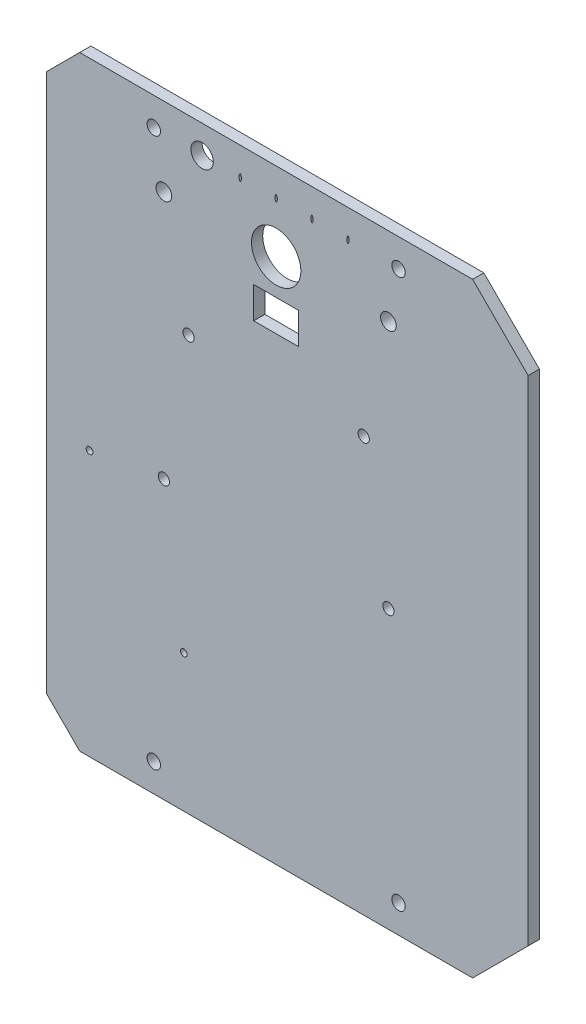
SolidWorks part; units mm, degrees
material "Alliage 1060"
ref_plane "Plan de dessus" through (0, 0, 0) normal (0, 0, 1) x (1, 0, 0)
ref_plane "Plan de droite" through (0, 0, 0) normal (0, 1, 0) x (1, 0, 0)
ref_plane "Plan de face" through (0, 0, 0) normal (1, 0, 0) x (0, 0, -1)
sketch "Esquisse1" plane through (0, 0, 0) normal (0, 0, 1) x (1, 0, 0)
  line L0 (0, 0) -> (-175, 0)
  line L1 (-175, 0) -> (-199.7487, 24.7487)
  line L2 (-199.7487, 24.7487) -> (-199.7487, 244.7487)
  line L3 (-199.7487, 244.7487) -> (-175, 269.4975)
  line L4 (-175, 269.4975) -> (0, 269.4975)
  line L5 (0, 269.4975) -> (24.7487, 244.7487)
  line L6 (24.7487, 244.7487) -> (24.7487, 24.7487)
  line L7 (24.7487, 24.7487) -> (0, 0)
  dimension "D1" = 220
  dimension "D2" = 35
  dimension "D3" = 135
  dimension "D4" = 175
extrude "Base" add sketch "Esquisse1" along normal blind 5
sketch "Esquisse2" plane through (0, 0, 5) normal (0, 0, 1) x (1, 0, 0)
  line L0 (-199.7487, 244.7487) -> (-199.7487, 24.7487) construction
  line L1 (-175, 0) -> (0, 0) construction
  line L2 (-199.7487, 134.7487) -> (24.7487, 134.7487) construction
  line L3 (24.7487, 24.7487) -> (24.7487, 244.7487) construction
  line L4 (-87.5, 269.4975) -> (-87.5, 0) construction
  line L5 (0, 269.4975) -> (-175, 269.4975) construction
  line L7 (-132.5, 179.7487) -> (-42.5, 179.7487) construction
  line L8 (-132.5, 179.7487) -> (-132.5, 89.7487) construction
  line L9 (-132.5, 89.7487) -> (-42.5, 89.7487) construction
  line L10 (-42.5, 179.7487) -> (-42.5, 89.7487) construction
  circle A0 centre (-141.9987, 12.5) radius 3
  circle A1 centre (-141.9987, 256.9975) radius 3
  circle A2 centre (-33.0013, 12.5) radius 3
  circle A3 centre (-33.0013, 256.9975) radius 3
  circle A4 centre (-137.5, 123.7487) radius 2.5
  circle A5 centre (-126.5, 184.7487) radius 2.5
  circle A6 centre (-37.5, 123.7487) radius 2.5
  circle A7 centre (-48.5, 184.7487) radius 2.5
  point P25 (-87.5, 179.7487)
  point P26 (-132.5, 134.7487)
  dimension "D1" = 6
  dimension "D6" = 5
  dimension "D8" = 5
  dimension "D2" = 57.75
  dimension "D3" = 12.5
  dimension "D4" = 90
  dimension "D5" = 34
  dimension "D7" = 5
  dimension "D9" = 5
  dimension "D10" = 6
  dimension "D11" = 90
sketch "Esquisse4" plane through (0, 0, 5) normal (0, 0, 1) x (1, 0, 0)
  line L0 (-87.5, 269.4975) -> (-87.5, 0) construction
  line L1 (0, 269.4975) -> (-175, 269.4975) construction
  line L2 (-132.5, 179.7487) -> (-42.5, 179.7487) construction
  line L3 (-97.5, 218.7487) -> (-77.5, 218.7487)
  line L4 (-97.5, 218.7487) -> (-97.5, 204.7487)
  line L5 (-97.5, 204.7487) -> (-77.5, 204.7487)
  line L6 (-77.5, 218.7487) -> (-77.5, 204.7487)
  line L7 (-87.5, 234.4975) -> (-37.5, 234.4975) construction
  line L8 (-87.5, 234.4975) -> (-137.5, 234.4975) construction
  line L9 (24.7487, 24.7487) -> (24.7487, 244.7487) construction
  circle A0 centre (-87.5, 234.4975) radius 11
  circle A1 centre (-137.5, 234.4975) radius 3.5
  circle A2 centre (-37.5, 234.4975) radius 3.5
  ellipse E0 centre (-103.5, 256.9975) end of major axis (-103.5, 255.4975) minor radius 0.5
  ellipse E5 centre (-87.5, 256.9975) end of major axis (-87.5, 255.4975) minor radius 0.5
  ellipse E6 centre (-71.5, 256.9975) end of major axis (-71.5, 255.4975) minor radius 0.5
  ellipse E7 centre (-55.5, 256.9975) end of major axis (-55.5, 255.4975) minor radius 0.5
  point P28 (-87.5, 218.7487)
  dimension "D4" = 22
  dimension "D7" = 7
  dimension "D1" = 3
  dimension "D2" = 1
  dimension "D3" = 16
  dimension "D5" = 35
  dimension "D8" = 35
  dimension "D10" = 25
  dimension "D11" = 14
  dimension "D12" = 20
  dimension "D13" = 100
  dimension "D14" = 37.5
  dimension "D6" = 4
  dimension "D9" = 2
sketch "Esquisse8" plane through (0, 0, 5) normal (0, 0, 1) x (1, 0, 0)
  circle A1 centre (-120.5, 256.9975) radius 5
  dimension "D3" = 10
  dimension "D4" = 17
extrude "Enlèv. mat.-Extru.7" cut sketch "Esquisse8" against normal blind 10
extrude "Enlèv. mat.-Extru.8" cut sketch "Esquisse4" against normal blind 10
extrude "Enlèv. mat.-Extru.9" cut sketch "Esquisse2" against normal blind 10
sketch "logo DVB" plane through (0, 0, 0) normal (0, 0, -1) x (-1, 0, 0)
  line L0 (87.5, 0) -> (87.5, 25) construction
  line L1 (175, 0) -> (0, 0) construction
sketch "Esquisse11" plane through (0, 0, 5) normal (0, 0, 1) x (1, 0, 0)
  line L0 (-170.6149, 118.1524) -> (-170.6149, 61.1524) construction
  line L1 (-170.6149, 61.1524) -> (-170.6149, 0) construction
  line L7 (-170.6149, 61.1524) -> (-128.6149, 61.1524) construction
  line L8 (-87.5, 269.4975) -> (-87.5, -98.2433) construction
  line L9 (0, 269.4975) -> (-175, 269.4975) construction
  line L10 (-189.7487, -12.261) -> (-189.7487, 134.7487)
  line L11 (-199.7487, -12.261) -> (-189.7487, -12.261)
  line L12 (-199.7487, 274.9208) -> (-199.7487, -12.261)
  line L13 (-189.7487, 274.9208) -> (-199.7487, 274.9208)
  line L14 (-189.7487, 134.7487) -> (-189.7487, 274.9208)
  line L15 (-175, 0) -> (0, 0) construction
  line L16 (-170.6149, 61.1524) -> (-199.7487, 61.1524) construction
  circle A0 centre (-170.6149, 118.1524) radius 1.5
  circle A1 centre (-128.6149, 61.1524) radius 1.5
  dimension "D3" = 3
  dimension "D1" = 42
  dimension "D2" = 57
  dimension "D4" = 61.1524
  dimension "D5" = 29.1338
extrude "Enlèv. mat.-Extru.11" cut sketch "Esquisse11" against normal blind 5
